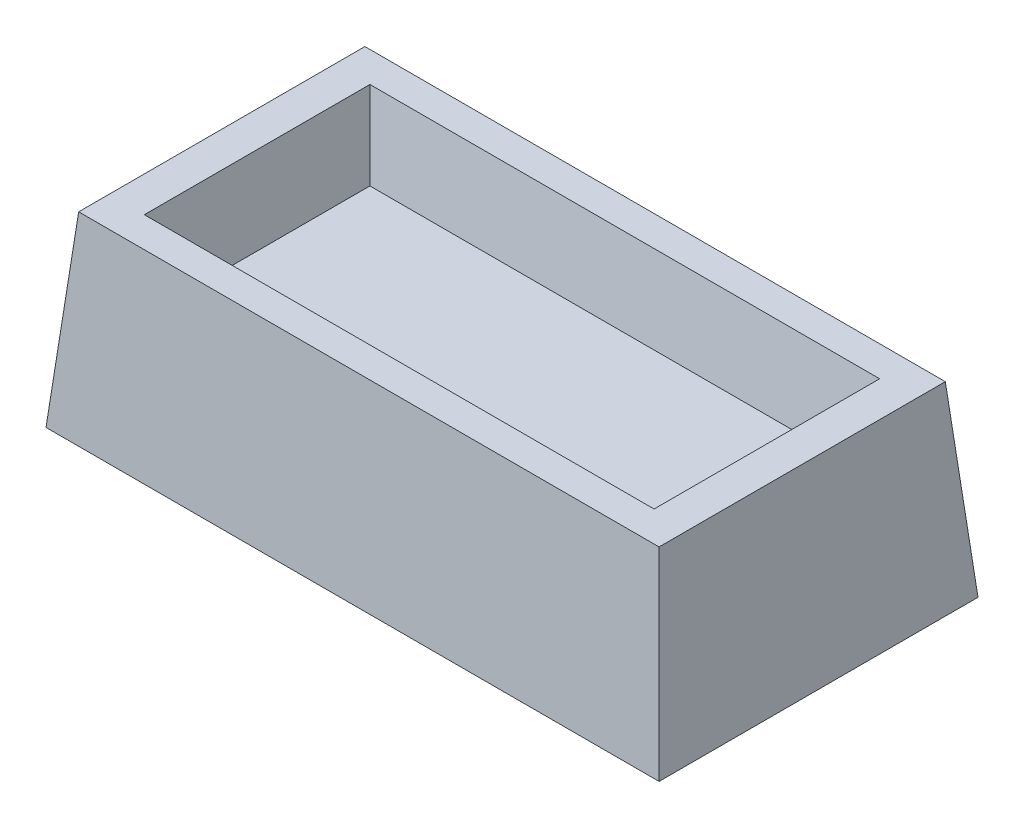
SolidWorks part; units mm, degrees
ref_plane "Front Plane" through (0, 0, 0) normal (0, 0, 1) x (1, 0, 0)
ref_plane "Top Plane" through (0, 0, 0) normal (0, 1, 0) x (1, 0, 0)
ref_plane "Right Plane" through (0, 0, 0) normal (1, 0, 0) x (0, 0, -1)
sketch "Sketch1" plane through (0, 0, 0) normal (0, 1, 0) x (1, 0, 0)
  line L1 (-82.0684, 42.6888) -> (82.0684, 42.6888)
  line L2 (-82.0684, 42.6888) -> (-82.0684, -42.6888)
  line L3 (-82.0684, -42.6888) -> (82.0684, -42.6888)
  line L4 (82.0684, 42.6888) -> (82.0684, -42.6888)
  line L5 (-82.0684, 42.6888) -> (82.0684, -42.6888) construction
  line L6 (-82.0684, -42.6888) -> (82.0684, 42.6888) construction
  point P0 (0, 0)
extrude "Boss-Extrude1" add sketch "Sketch1" along normal blind 50 draft 5 contours L2 L1 L4 L3
sketch "Sketch2" plane through (0, 50, 0) normal (0, 1, 0) x (1, 0, 0)
  line L1 (-68.2339, 30.1955) -> (68.2339, 30.1955)
  line L2 (-68.2339, 30.1955) -> (-68.2339, -30.1955)
  line L3 (-68.2339, -30.1955) -> (68.2339, -30.1955)
  line L4 (68.2339, 30.1955) -> (68.2339, -30.1955)
  line L5 (-68.2339, 30.1955) -> (68.2339, -30.1955) construction
  line L6 (-68.2339, -30.1955) -> (68.2339, 30.1955) construction
  point P0 (0, 0)
extrude "Cut-Extrude1" cut sketch "Sketch2" against normal blind 20 draft 10
shell "Shell1" thickness 3
